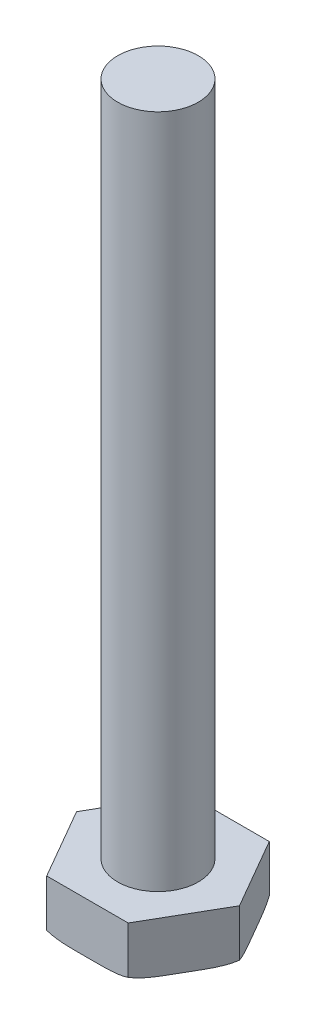
SolidWorks part; units mm, degrees
ref_plane "Front Plane" through (0, 0, 0) normal (0, 0, 1) x (1, 0, 0)
ref_plane "Top Plane" through (0, 0, 0) normal (0, 1, 0) x (1, 0, 0)
ref_plane "Right Plane" through (0, 0, 0) normal (1, 0, 0) x (0, 0, -1)
sketch "Sketch1" plane through (0, 0, 0) normal (0, 1, 0) x (1, 0, 0)
  line L1 (6.4158, 0) -> (3.2079, 5.5563)
  line L2 (3.2079, 5.5563) -> (-3.2079, 5.5562)
  line L3 (-3.2079, 5.5562) -> (-6.4158, 0)
  line L4 (-6.4158, 0) -> (-3.2079, -5.5563)
  line L5 (-3.2079, -5.5563) -> (3.2079, -5.5562)
  line L6 (3.2079, -5.5562) -> (6.4158, 0)
  circle A0 centre (0, 0) radius 5.5562 construction
  dimension "D1" = 11.1125
  dimension "D2" = 5.5562
extrude "Boss-Extrude1" add sketch "Sketch1" along normal blind 3.9688
sketch "Sketch2" plane through (0, 0, 0) normal (0, 0, 1) x (1, 0, 0)
  line L0 (0, 0) -> (0, 4.1401) construction
  line L1 (0, -2.2771) -> (0, 2.2771) construction
  line L2 (0, 0) -> (5.5925, 0) construction
  line L3 (6.4158, 3.9688) -> (6.4158, 0) construction
  line L4 (6.4158, 0.254) -> (6.4158, 0)
  line L5 (6.1119, 0) -> (-6.1119, 0) construction
  line L6 (6.4158, 0) -> (5.5925, 0)
  arc A0 (5.5925, 0) -> (6.4158, 0.254) centre (5.5925, 1.4613) ccw
  dimension "D2" = 1.4613
  dimension "D3" = 0.254
  dimension "D1" = 4.1401
revolve "Cut-Revolve1" cut sketch "Sketch2" angle 360 about L0
sketch "Sketch3" plane through (0, 0, 0) normal (0, 1, 0) x (1, 0, 0)
  circle A0 centre (0, 0) radius 3.175
  dimension "D1" = 6.35
extrude "Boss-Extrude2" add sketch "Sketch3" along normal blind 57.15
